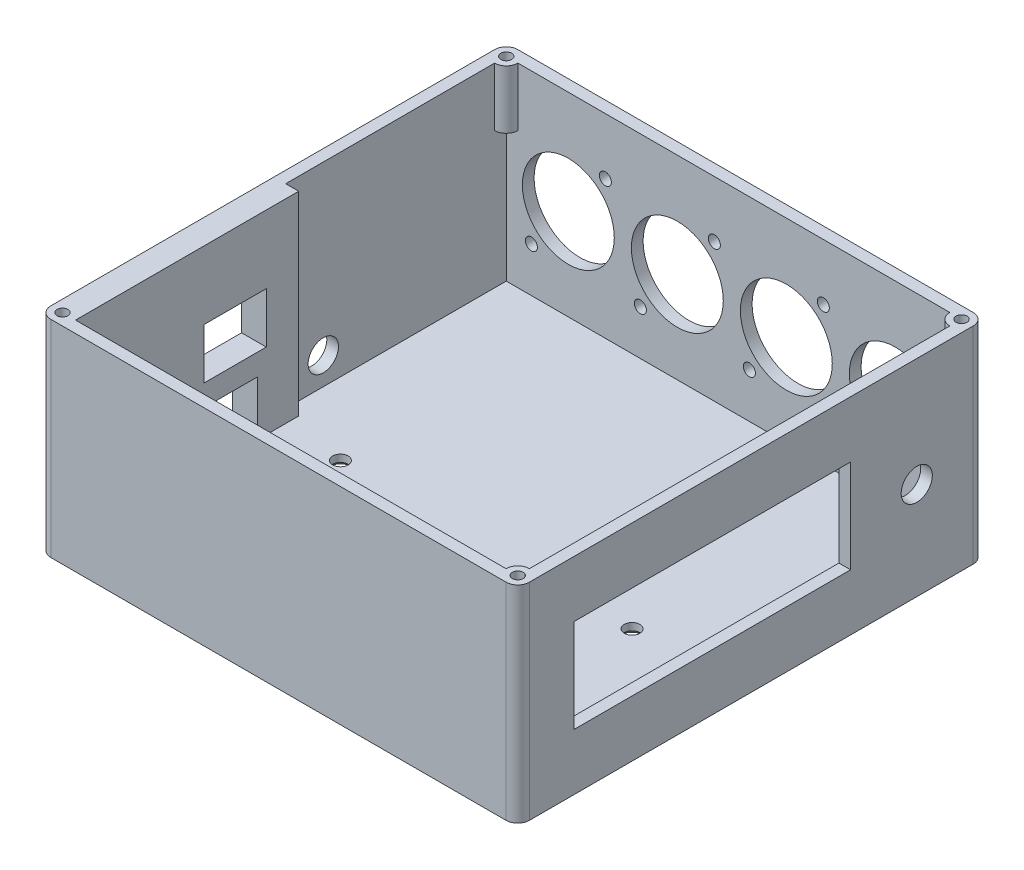
SolidWorks part; units mm, degrees
ref_plane "Front Plane" through (0, 0, 0) normal (0, 0, 1) x (1, 0, 0)
ref_plane "Top Plane" through (0, 0, 0) normal (0, 1, 0) x (1, 0, 0)
ref_plane "Right Plane" through (0, 0, 0) normal (1, 0, 0) x (0, 0, -1)
sketch "Sketch1" plane through (0, 0, 0) normal (0, 1, 0) x (1, 0, 0)
  line L1 (-50.8, -26.67) -> (50.8, -26.67)
  line L2 (-50.8, -26.67) -> (-50.8, 26.67)
  line L3 (-50.8, 26.67) -> (50.8, 26.67)
  line L4 (50.8, -26.67) -> (50.8, 26.67)
  line L5 (-50.8, -26.67) -> (50.8, 26.67) construction
  line L6 (-50.8, 26.67) -> (50.8, -26.67) construction
  line L7 (-57.15, -31.67) -> (65.8, -31.67)
  line L8 (-57.15, -31.67) -> (-57.15, 88.33)
  line L9 (-57.15, 88.33) -> (65.8, 88.33)
  line L10 (65.8, -31.67) -> (65.8, 88.33)
  circle A0 centre (-35.56, 24.13) radius 2
  circle A1 centre (-36.83, -24.13) radius 2
  circle A2 centre (45.72, -24.13) radius 2
  circle A3 centre (39.37, 24.13) radius 2
  point P0 (0, 0)
  dimension "D3" = 13.97
  dimension "D8" = 50.8
  dimension "D1" = 53.34
  dimension "D2" = 101.6
  dimension "D4" = 2.54
  dimension "D5" = 2.54
  dimension "D6" = 96.52
  dimension "D7" = 15.24
  dimension "D9" = 50.8
  dimension "D10" = 90.17
  dimension "D11" = 6.35
  dimension "D12" = 5
  dimension "D13" = 15
  dimension "D14" = 120
extrude "Boss-Extrude1" add sketch "Sketch1" along normal blind 3 contours L7 L10 L9 L8 L4 L1 L2 L3 | L1 L4 L3 L2 A3 A2 A1 A0
sketch "Sketch2" plane through (0, 3, 0) normal (0, 1, 0) x (1, 0, 0)
  line L1 (-50.8, 85.33) -> (62.8, 85.33)
  line L2 (-50.8, 85.33) -> (-50.8, -28.67)
  line L3 (-50.8, -28.67) -> (62.8, -28.67)
  line L4 (62.8, 85.33) -> (62.8, -28.67)
  line L5 (-57.15, 88.33) -> (65.8, 88.33)
  line L6 (-57.15, 88.33) -> (-57.15, -31.67)
  line L7 (-57.15, -31.67) -> (65.8, -31.67)
  line L8 (65.8, 88.33) -> (65.8, -31.67)
  dimension "D1" = 6.35
  dimension "D2" = 3
  dimension "D3" = 3
  dimension "D4" = 3
extrude "Boss-Extrude2" add sketch "Sketch2" along normal blind 50
sketch "Sketch3" plane through (-50.8, 0, 0) normal (1, 0, 0) x (0, 0, -1)
  line L0 (85.33, 53) -> (-28.67, 53) construction
  line L1 (85.33, 3) -> (28.67, 3)
  line L2 (85.33, 3) -> (85.33, 53)
  line L3 (85.33, 53) -> (28.67, 53)
  line L4 (28.67, 3) -> (28.67, 53)
  line L5 (-28.67, 53) -> (-28.67, 3) construction
  dimension "D1" = 57.34
extrude "Cut-Extrude1" cut sketch "Sketch3" against normal blind 3.35
sketch "Sketch4" plane through (-50.8, 0, 0) normal (1, 0, 0) x (0, 0, -1)
  line L0 (-28.67, 53) -> (-28.67, 3) construction
  line L1 (5.33, 6) -> (18.03, 6)
  line L2 (5.33, 6) -> (5.33, 17)
  line L3 (5.33, 17) -> (18.03, 17)
  line L4 (18.03, 6) -> (18.03, 17)
  line L5 (28.67, 3) -> (-28.67, 3) construction
  line L7 (4.33, 35.5) -> (20.33, 35.5)
  line L8 (4.33, 35.5) -> (4.33, 22.5)
  line L9 (4.33, 22.5) -> (20.33, 22.5)
  line L10 (20.33, 35.5) -> (20.33, 22.5)
  dimension "D1" = 34
  dimension "D2" = 12.7
  dimension "D3" = 11
  dimension "D4" = 3
  dimension "D5" = 33
  dimension "D6" = 16
  dimension "D7" = 13
  dimension "D8" = 5.5
extrude "Cut-Extrude2" cut sketch "Sketch4" against normal blind 7
sketch "Sketch5" plane through (-50.8, 0, 0) normal (1, 0, 0) x (0, 0, -1)
  line L0 (28.67, 3) -> (-28.67, 3) construction
  line L1 (-23.495, 17) -> (-14.605, 17)
  line L2 (-23.495, 17) -> (-23.495, 6)
  line L3 (-23.495, 6) -> (-14.605, 6)
  line L4 (-14.605, 17) -> (-14.605, 6)
  line L5 (-28.67, 53) -> (-28.67, 3) construction
  dimension "D1" = 8.89
  dimension "D2" = 3
  dimension "D3" = 5.175
  dimension "D4" = 11
extrude "Cut-Extrude3" cut sketch "Sketch5" against normal blind 2.54
sketch "Sketch6" plane through (65.8, 0, 0) normal (1, 0, 0) x (0, 0, -1)
  line L0 (-31.67, 0) -> (88.33, 0) construction
  line L1 (-17.17, 38.5) -> (53.83, 38.5)
  line L2 (-17.17, 38.5) -> (-17.17, 14.5)
  line L3 (-17.17, 14.5) -> (53.83, 14.5)
  line L4 (53.83, 38.5) -> (53.83, 14.5)
  line L5 (-31.67, 53) -> (-31.67, 0) construction
  circle A0 centre (70.83, 25) radius 4
  dimension "D5" = 25
  dimension "D6" = 17
  dimension "D1" = 71
  dimension "D2" = 24
  dimension "D3" = 14.5
  dimension "D4" = 14.5
extrude "Cut-Extrude4" cut sketch "Sketch6" against normal blind 5
sketch "Sketch7" plane through (0, 0, -88.33) normal (0, 0, -1) x (-1, 0, 0)
  line L0 (57.15, 0) -> (-65.8, 0) construction
  line L1 (-65.8, 53) -> (-65.8, 0) construction
  circle A0 centre (-45.8, 26.5) radius 11.8
  circle A1 centre (-55.3, 38.5) radius 1.55
  circle A2 centre (-36.3, 14.5) radius 1.55
  circle A3 centre (-17.8, 26.5) radius 11.8
  circle A4 centre (-27.3, 38.5) radius 1.55
  circle A5 centre (-8.3, 14.5) radius 1.55
  circle A6 centre (10.2, 26.5) radius 11.8
  circle A7 centre (0.7, 38.5) radius 1.55
  circle A8 centre (19.7, 14.5) radius 1.55
  circle A9 centre (38.2, 26.5) radius 11.8
  circle A10 centre (28.7, 38.5) radius 1.55
  circle A11 centre (47.7, 14.5) radius 1.55
  dimension "D1" = 9.5
  dimension "D2" = 9.5
  dimension "D3" = 12
  dimension "D4" = 12
  dimension "D5" = 26.5
  dimension "D6" = 20
  dimension "D7" = 4
extrude "Cut-Extrude5" cut sketch "Sketch7" against normal blind 5
hole_wizard "CSK for M3 Flat Head Machine Screw1" positions "Sketch9" profile "Sketch8" countersink size "M3" standard "ANSI Metric" end condition through all
sketch "Sketch9" plane through (0, 0, 0) normal (0, -1, 0) x (-1, 0, 0)
  point P0 (36.83, -24.13)
  point P3 (-45.72, -24.13)
  point P6 (35.56, 24.13)
  point P9 (-39.37, 24.13)
sketch "Sketch8" plane through (-36.83, 0, 24.13) normal (1, 0, 0) x (0, 0, -1)
  line L0 (0, 0) -> (0, 53)
  line L1 (0, 53) -> (1.7, 53)
  line L2 (1.7, 53) -> (1.7, 1.45)
  line L3 (1.7, 1.45) -> (3.15, 0)
  line L5 (3.15, 0) -> (0, 0)
  line L6 (-1.7, 1.45) -> (-3.15, 0) construction
  line L11 (0, -6.35) -> (0, 107.95) construction
  dimension "Thru Hole Dia." = 3.4
  dimension "Thru Hole Depth" = 53
  dimension "Near C'Sink Dia." = 6.3
  dimension "Near C'Sink Angle" = 90
fillet "Fillet1" radius 3 4 edges at (-57.15, 26.5, 31.67) (-57.15, 26.5, -88.33) (65.8, 26.5, -88.33) (65.8, 26.5, 31.67)
sketch "Sketch10" plane through (-57.15, 0, 0) normal (-1, 0, 0) x (0, 0, 1)
  line L0 (28.67, 0) -> (-85.33, 0) construction
  line L1 (-88.33, 0) -> (-88.33, 53) construction
  circle A0 centre (-38.33, 10) radius 3.9
  dimension "D1" = 10
  dimension "D2" = 50
extrude "Cut-Extrude6" cut sketch "Sketch10" against normal blind 5
sketch "Sketch11" plane through (0, 53, 0) normal (0, 1, 0) x (1, 0, 0)
  circle A0 centre (-54.15, 85.33) radius 3
  circle A1 centre (62.8, 85.33) radius 3
  circle A2 centre (62.8, -28.67) radius 3
  circle A3 centre (-54.15, -28.67) radius 3
extrude "Boss-Extrude3" add sketch "Sketch11" against normal blind 15
sketch "Sketch12" plane through (0, 53, 0) normal (0, 1, 0) x (1, 0, 0)
  line L0 (62.8, 88.33) -> (-54.15, 88.33) construction
  line L1 (-57.15, 85.33) -> (-57.15, -28.67) construction
  line L2 (65.8, -28.67) -> (65.8, 85.33) construction
  line L3 (-54.15, -31.67) -> (62.8, -31.67) construction
  circle A0 centre (-54.15, 85.33) radius 1.4
  circle A1 centre (62.8, 85.33) radius 1.4
  circle A2 centre (62.8, -28.67) radius 1.4
  circle A3 centre (-54.15, -28.67) radius 1.4
  dimension "D1" = 3
  dimension "D2" = 3
  dimension "D3" = 3
  dimension "D4" = 3
  dimension "D5" = 3
  dimension "D6" = 3
extrude "Cut-Extrude7" cut sketch "Sketch12" against normal blind 12
sketch "Sketch13" plane through (0, 0, -88.33) normal (0, 0, -1) x (-1, 0, 0)
  line L0 (-57.6, 26.5) -> (-6, 26.5) construction
  line L1 (-57.6, 43.5) -> (-6, 43.5) construction
  line L2 (-1.6, 26.5) -> (50, 26.5) construction
  line L3 (-1.6, 43.5) -> (50, 43.5) construction
  circle A0 centre (-45.8, 26.5) radius 11.8 construction
  circle A1 centre (-17.8, 26.5) radius 11.8 construction
  circle A2 centre (10.2, 26.5) radius 11.8 construction
  circle A3 centre (38.2, 26.5) radius 11.8 construction
  circle A4 centre (-55.3, 38.5) radius 1.55 construction
  circle A5 centre (0.7, 38.5) radius 1.55 construction
  text T0 "--------- Universe 1 ---------"
  text T1 "--------- Universe 2 ---------"
  dimension "D1" = 5
  dimension "D2" = 5
extrude "Cut-Extrude8" cut sketch "Sketch13" against normal blind 1
sketch "Sketch14" plane through (-57.15, 0, 0) normal (-1, 0, 0) x (0, 0, 1)
  line L0 (-42.23, 10) -> (-34.43, 10) construction
  line L1 (-42.23, 16) -> (-34.43, 16) construction
  circle A0 centre (-38.33, 10) radius 3.9 construction
  text T0 "18V"
  dimension "D1" = 6
extrude "Cut-Extrude9" cut sketch "Sketch14" against normal blind 1
